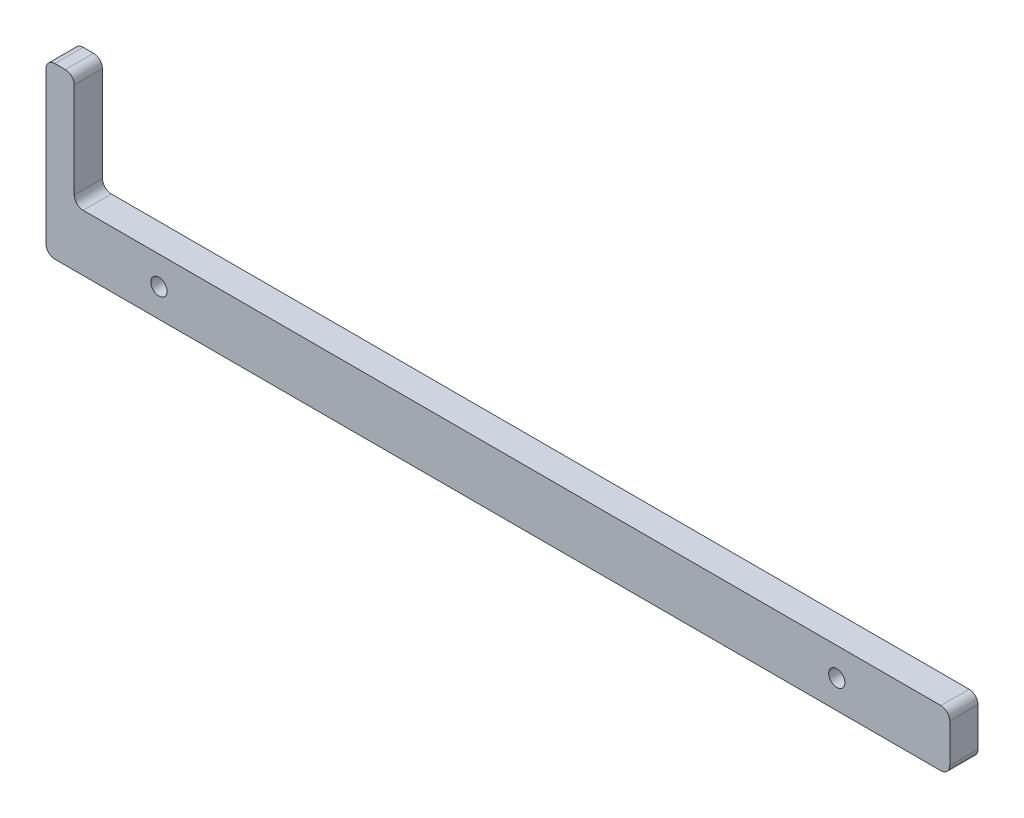
SolidWorks part; units mm, degrees
ref_plane "Front Plane" through (0, 0, 0) normal (0, 0, 1) x (1, 0, 0)
ref_plane "Top Plane" through (0, 0, 0) normal (0, 1, 0) x (1, 0, 0)
ref_plane "Right Plane" through (0, 0, 0) normal (1, 0, 0) x (0, 0, -1)
sketch "Sketch2" plane through (0, 0, 0) normal (0, 0, 1) x (1, 0, 0)
  line L1 (0, 0) -> (203.2, 0)
  line L2 (0, 0) -> (0, 12.7)
  line L3 (0, 12.7) -> (203.2, 12.7)
  line L4 (203.2, 0) -> (203.2, 12.7)
  dimension "D1" = 12.7
  dimension "D2" = 203.2
extrude "Boss-Extrude1" add sketch "Sketch2" along normal blind 6.35
sketch "Sketch3" plane through (0, 12.7, 0) normal (0, 1, 0) x (1, 0, 0)
  line L0 (203.2, -6.35) -> (0, -6.35) construction
  line L1 (0, 0) -> (6.35, 0)
  line L2 (0, 0) -> (0, -6.35)
  line L3 (0, -6.35) -> (6.35, -6.35)
  line L4 (6.35, 0) -> (6.35, -6.35)
  dimension "D1" = 6.35
extrude "Boss-Extrude2" add sketch "Sketch3" along normal blind 25.4
fillet "Fillet2" radius 2 6 edges at (0, 0, 3.175) (0, 38.1, 3.175) (6.35, 12.7, 3.175) (203.2, 0, 3.175) (203.2, 12.7, 3.175) (6.35, 38.1, 3.175)
hole_wizard "#6 Clearance Hole1" positions "Sketch4" profile "Sketch5" hole size "#6" standard "ANSI Inch"
sketch "Sketch4" plane through (0, 0, 6.35) normal (0, 0, 1) x (1, 0, 0)
  line L0 (203.2, 6.35) -> (0, 6.35) construction
  line L1 (203.2, 2) -> (203.2, 10.7) construction
  line L2 (0, 36.1) -> (0, 2) construction
  point P9 (25.4, 6.35)
  point P11 (177.8, 6.35)
  dimension "D1" = 25.4
  dimension "D2" = 25.4
sketch "Sketch5" plane through (177.8, 6.35, 6.35) normal (1, 0, 0) x (0, -1, 0)
  line L0 (0, 0) -> (0, 11.2589)
  line L1 (0, 11.2589) -> (1.8288, 10.16)
  line L2 (1.8288, 10.16) -> (1.8288, 0)
  line L5 (1.8288, 0) -> (0, 0)
  line L10 (0, 11.2589) -> (-1.8288, 10.16) construction
  line L11 (0, -6.35) -> (0, 107.95) construction
  dimension "Hole Dia." = 3.6576
  dimension "Hole Depth" = 10.16
  dimension "Drill Angle" = 118
